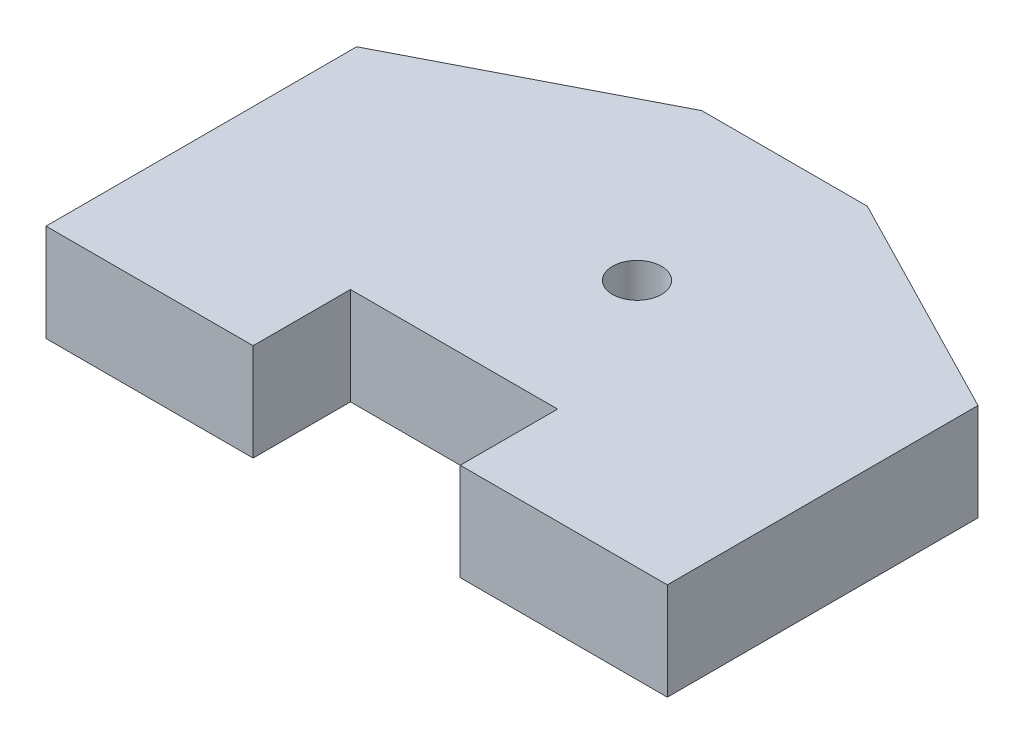
SolidWorks part; units mm, degrees
ref_plane "Front Plane" through (0, 0, 0) normal (0, 0, 1) x (1, 0, 0)
ref_plane "Top Plane" through (0, 0, 0) normal (0, 1, 0) x (1, 0, 0)
ref_plane "Right Plane" through (0, 0, 0) normal (1, 0, 0) x (0, 0, -1)
sketch "Sketch1" plane through (0, 0, 0) normal (0, 1, 0) x (1, 0, 0)
  line L0 (0, 19.05) -> (13.97, 26.2387)
  line L1 (0, 0) -> (12.7, 0)
  line L2 (0, 0) -> (0, 19.05)
  line L3 (13.97, 26.2387) -> (24.13, 26.2387)
  line L4 (38.1, 0) -> (38.1, 19.05)
  line L5 (25.4, 0) -> (38.1, 0)
  line L6 (21, 15.24) -> (38.1, 15.24) construction
  line L7 (38.1, 19.05) -> (24.13, 26.2387)
  line L8 (12.7, 0) -> (12.7, 5.969)
  line L9 (12.7, 5.969) -> (25.4, 5.969)
  line L10 (25.4, 5.969) -> (25.4, 0)
  circle A0 centre (21, 15.24) radius 1.5
  dimension "D6" = 3
  dimension "D1" = 38.1
  dimension "D2" = 5.969
  dimension "D3" = 10.16
  dimension "D4" = 7.1887
  dimension "D5" = 19.05
  dimension "D7" = 21
  dimension "D8" = 15.24
extrude "Boss-Extrude1" add sketch "Sketch1" along normal blind 5.969
